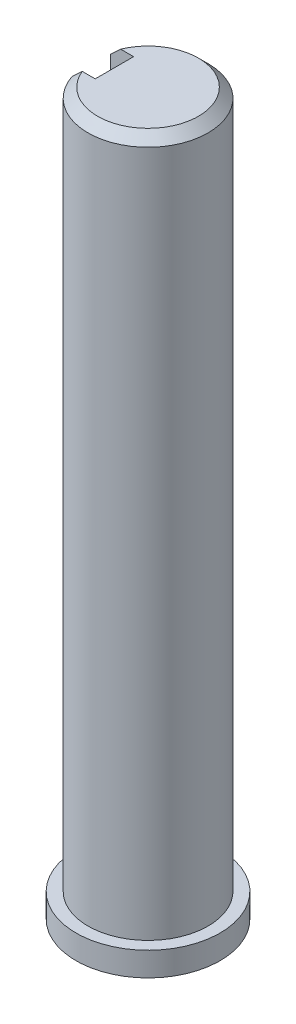
SolidWorks part; units mm, degrees
ref_plane "Front Plane" through (0, 0, 0) normal (0, 0, 1) x (1, 0, 0)
ref_plane "Top Plane" through (0, 0, 0) normal (0, 1, 0) x (1, 0, 0)
ref_plane "Right Plane" through (0, 0, 0) normal (1, 0, 0) x (0, 0, -1)
sketch "Sketch1" plane through (0, 0, 0) normal (0, 0, 1) x (1, 0, 0)
  line L0 (0, 0) -> (0, 150) construction
  line L1 (0, 150) -> (12.5, 150)
  line L6 (12.5, 150) -> (12.5, 5)
  line L7 (12.5, 5) -> (15, 5)
  line L8 (15, 5) -> (15, 0)
  line L9 (15, 0) -> (0, 0)
  line L10 (0, 0) -> (0, 150)
  dimension "D1" = 25
  dimension "D4" = 5
  dimension "D5" = 150
  dimension "D8" = 30
revolve "Revolve1" add sketch "Sketch1" angle 360 about L0
sketch "Esboço3" plane through (0, 150, 0) normal (0, 1, 0) x (1, 0, 0)
  line L0 (0, 0) -> (-16.2444, 0) construction
  line L2 (-7, 4) -> (-15, 4)
  line L3 (-7, 4) -> (-7, -4)
  line L4 (-7, -4) -> (-15, -4)
  line L5 (-15, 4) -> (-15, -4)
  line L6 (-7, 4) -> (-15, -4) construction
  line L7 (-7, -4) -> (-15, 4) construction
  circle A2 centre (0, 0) radius 15 construction
  point P4 (-11, 0)
  dimension "D1" = 8
  dimension "D2" = 8
  dimension "D3" = 8
extrude "Corte-extrusão1" cut sketch "Esboço3" against normal blind 20
chamfer "Chanfro1" distance 2 angle 45 1 edges at (12.5, 150, 0)
